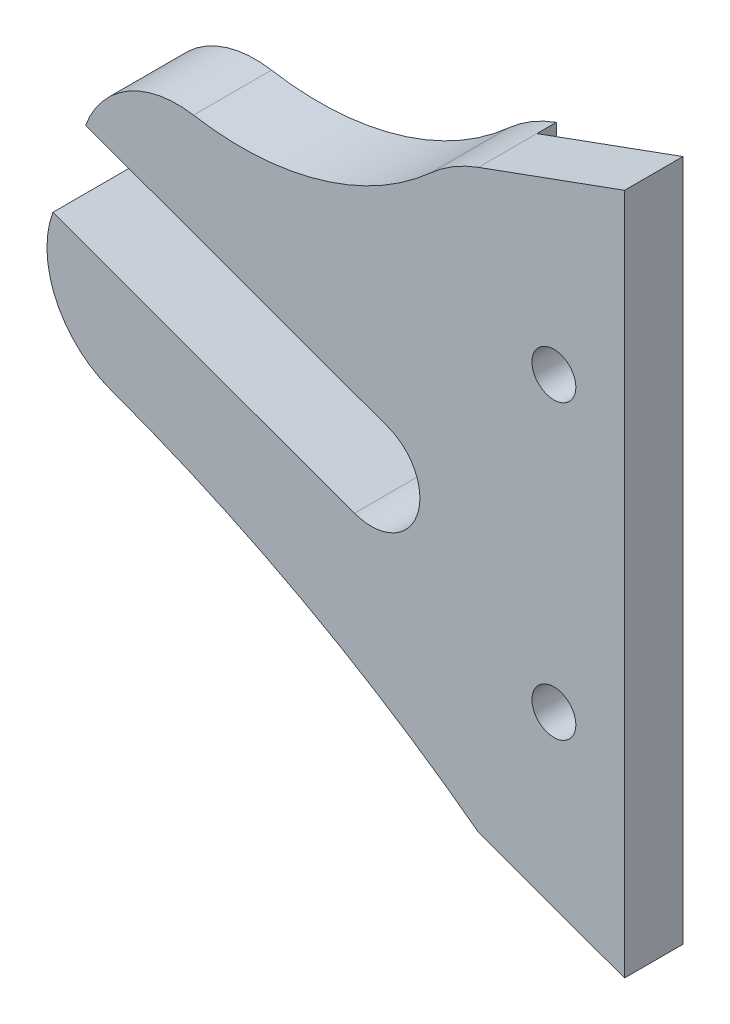
SolidWorks part; units mm, degrees
ref_plane "Plan de face" through (0, 0, 0) normal (0, 0, 1) x (1, 0, 0)
ref_plane "Plan de dessus" through (0, 0, 0) normal (0, 1, 0) x (1, 0, 0)
ref_plane "Plan de droite" through (0, 0, 0) normal (1, 0, 0) x (0, 0, -1)
sketch "Esquisse1" plane through (0, 0, 0) normal (0, 0, 1) x (1, 0, 0)
  line L0 (34.3468, -30.2565) -> (34.3468, 39.7435)
  line L1 (19.3468, 34.2839) -> (34.3468, 39.7435)
  line L2 (34.3468, -30.2565) -> (19.3468, -24.797)
  line L3 (10.0569, 6.5843) -> (-20.953, 17.8709)
  line L4 (-24.3171, 8.4536) -> (6.6367, -2.8127)
  arc A0 (10.0569, 6.5843) -> (6.6367, -2.8127) centre (8.3468, 1.8858) cw
  arc A1 (-24.3171, 8.4536) -> (-18.3403, -4.3635) centre (-14.9201, 5.0334) ccw
  arc A2 (-18.3403, -4.3635) -> (19.3468, -24.797) centre (-68.1376, -141.1805) cw
  arc A4 (-20.953, 17.8709) -> (-9.8823, 24.3097) centre (-11.556, 14.4507) cw
  arc A5 (19.3468, 34.2839) -> (14.4581, 31.3519) centre (24.4771, 20.1885) ccw
  arc A6 (14.4581, 31.3519) -> (-9.8823, 24.3097) centre (-5.0051, 53.0381) cw
  point P14 (0, 0)
  point P22 (34.3468, -2.2565)
  dimension "D8" = 33
  dimension "D10" = 15
  dimension "D12" = 10
  dimension "D9" = 10
  dimension "D2" = 70
  dimension "D3" = 70
  dimension "D4" = 42
  dimension "D5" = 10
  dimension "D6" = 26
  dimension "D13" = 70
extrude "Extrusion1" add sketch "Esquisse1" along normal blind 8
sketch "Esquisse5" plane through (0, 0, 0) normal (0, 0, -1) x (-1, 0, 0)
  line L0 (-34.3468, -30.2565) -> (-34.3468, 39.7435) construction
  line L1 (-36.4386, 42.157) -> (-19.3468, 42.157)
  line L2 (-36.4386, 42.157) -> (-36.4386, -34.8233)
  line L3 (-36.4386, -34.8233) -> (-19.3468, -34.8233)
  line L4 (-19.3468, 42.157) -> (-19.3468, -34.8233)
  dimension "D1" = 15
extrude "Extrusion3" cut sketch "Esquisse5" against normal blind 2
sketch "Esquisse6" plane through (0, 0, 2) normal (0, 0, -1) x (-1, 0, 0)
  line L0 (-19.3468, -24.797) -> (-19.3468, 34.2839) construction
  circle A0 centre (-27.0968, 19.7435) radius 2.25
  circle A1 centre (-27.0968, -10.2565) radius 2.25
  dimension "D1" = 4.5
  dimension "D2" = 4.5
  dimension "D3" = 7.75
  dimension "D4" = 7.75
  dimension "D5" = 20
  dimension "D6" = 30
extrude "Extrusion4" cut sketch "Esquisse6" against normal through all
